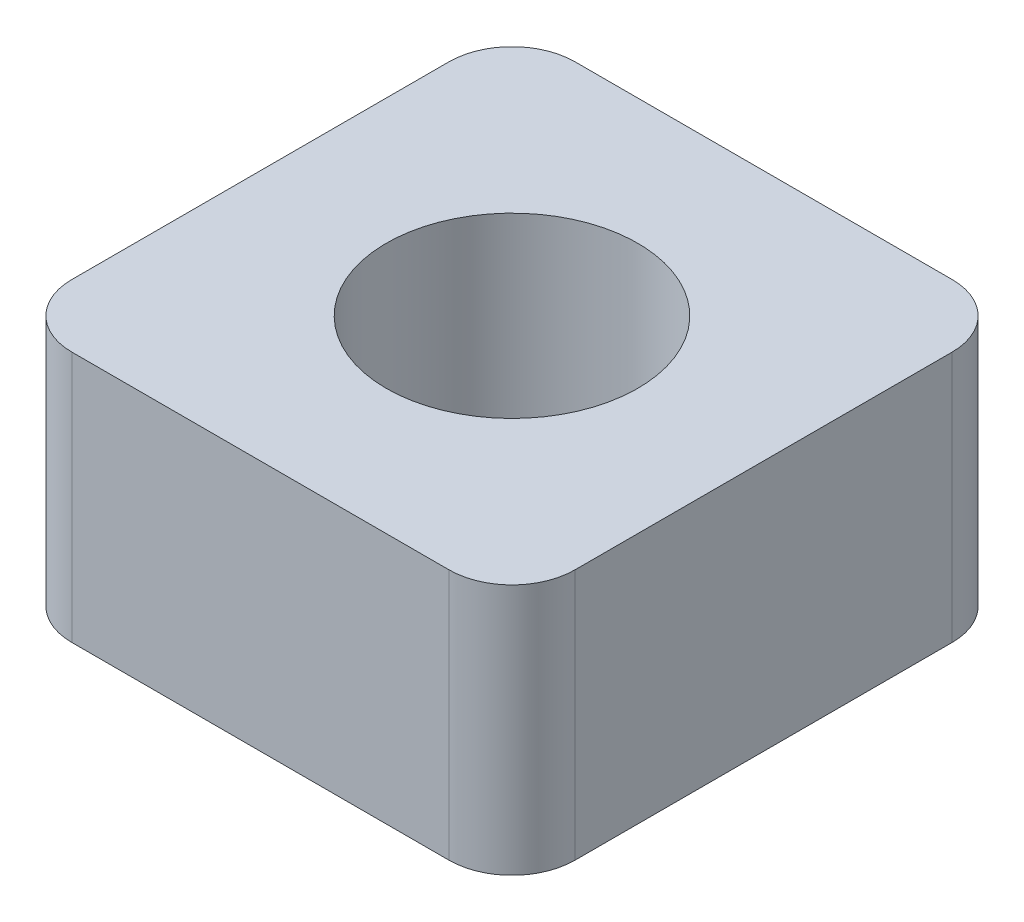
SolidWorks part; units mm, degrees
material "不锈钢 (铁素体)"
ref_plane "前视基准面" through (0, 0, 0) normal (0, 0, 1) x (1, 0, 0)
ref_plane "上视基准面" through (0, 0, 0) normal (0, 1, 0) x (1, 0, 0)
ref_plane "右视基准面" through (0, 0, 0) normal (1, 0, 0) x (0, 0, -1)
sketch "草图1" plane through (0, 0, 0) normal (0, 1, 0) x (1, 0, 0)
  line L1 (-4, 4) -> (4, 4)
  line L2 (-4, 4) -> (-4, -4)
  line L3 (-4, -4) -> (4, -4)
  line L4 (4, 4) -> (4, -4)
  line L5 (-4, 4) -> (4, -4) construction
  line L6 (-4, -4) -> (4, 4) construction
  circle A0 centre (0, 0) radius 2
  dimension "D1" = 8
  dimension "D3" = 4
  dimension "D2" = 8
extrude "凸台-拉伸1" add sketch "草图1" along normal blind 4
fillet "圆角1" radius 1 4 edges at (4, 2, 4) (4, 2, -4) (-4, 2, -4) (-4, 2, 4)
sketch "草图2" plane through (-4, 0, 0) normal (-1, 0, 0) x (0, 0, 1)
  line L0 (0, 0) -> (0, 4) construction
  line L1 (-3, 4) -> (3, 4) construction
  circle A0 centre (0, 2) radius 1.5 construction
